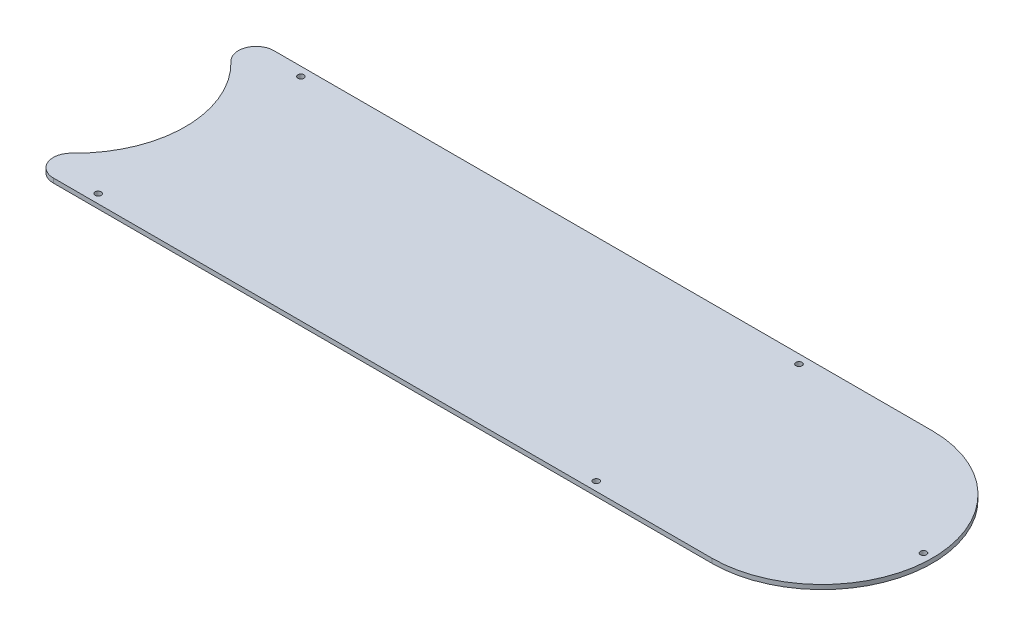
SolidWorks part; units mm, degrees
ref_plane "Front Plane" through (0, 0, 0) normal (0, 0, 1) x (1, 0, 0)
ref_plane "Top Plane" through (0, 0, 0) normal (0, 1, 0) x (1, 0, 0)
ref_plane "Right Plane" through (0, 0, 0) normal (1, 0, 0) x (0, 0, -1)
sketch "Sketch1" plane through (0, 0, 0) normal (0, 1, 0) x (1, 0, 0)
  line L0 (0, 0) -> (266.7, 0) construction
  line L1 (266.7, 39.37) -> (0, 39.37)
  line L2 (0, -39.37) -> (266.7, -39.37)
  arc A0 (0, -39.37) -> (0, 39.37) centre (0, 0) ccw
  arc A1 (266.7, -39.37) -> (266.7, 39.37) centre (266.7, 0) ccw
  circle A2 centre (302.895, 0) radius 1.0922
  circle A3 centre (222.25, 36.195) radius 1.0922
  circle A4 centre (44.45, 36.195) radius 1.0922
  circle A5 centre (44.45, -36.195) radius 1.0922
  circle A6 centre (222.25, -36.195) radius 1.0922
  dimension "D1" = 78.74
  dimension "D3" = 2.1844
  dimension "D2" = 266.7
  dimension "D4" = 3.175
  dimension "D5" = 3.175
  dimension "D6" = 44.45
  dimension "D7" = 44.45
extrude "Boss-Extrude1" add sketch "Sketch1" along normal blind 1.5875
fillet "Fillet1" radius 6.35 2 edges at (0, 0.7937, 39.37) (0, 0.7937, -39.37)
